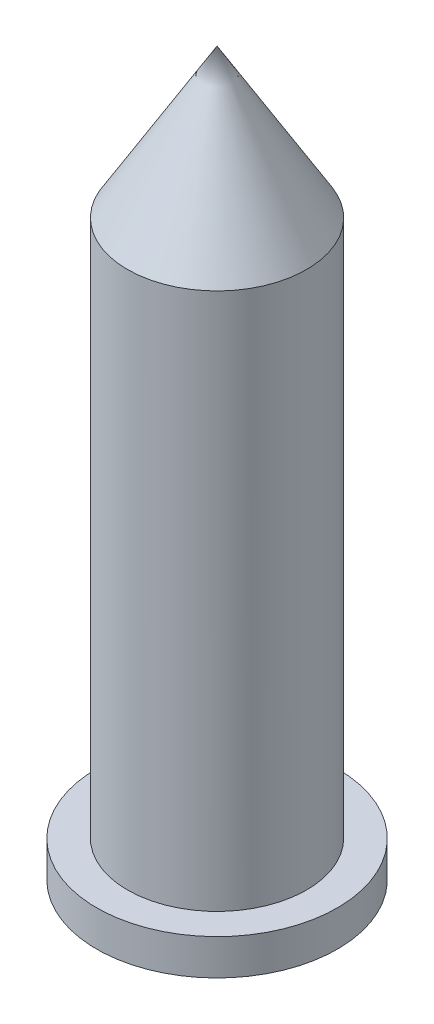
SolidWorks part; units mm, degrees
ref_plane "Front" through (0, 0, 0) normal (0, 0, 1) x (1, 0, 0)
ref_plane "Top" through (0, 0, 0) normal (0, 1, 0) x (1, 0, 0)
ref_plane "Right" through (0, 0, 0) normal (1, 0, 0) x (0, 0, -1)
sketch "Sketch1" plane through (0, 0, 0) normal (1, 0, 0) x (0, 0, -1)
  line L1 (-27.9083, 64.6906) -> (-22.9083, 64.6906)
  line L2 (-27.9083, 64.6906) -> (-27.9083, 34.6906)
  line L3 (-27.9083, 34.6906) -> (-22.9083, 34.6906)
  line L4 (-22.9083, 64.6906) -> (-22.9083, 34.6906)
  line L5 (-25.4083, 34.6906) -> (-25.4083, 64.6906) construction
  line L6 (-27.9083, 49.6906) -> (-22.9083, 49.6906) construction
  point P0 (-25.4083, 49.6906)
  dimension "D1" = 30
  dimension "D2" = 5
revolve "Revolve1" add sketch "Sketch1" angle 360 about L4
sketch "Sketch2" plane through (0, 0, 0) normal (1, 0, 0) x (0, 0, -1)
  line L0 (-17.9083, 64.6906) -> (-27.9083, 64.6906) construction
  line L1 (-27.9083, 64.6906) -> (-22.9083, 72.9987)
  line L2 (-22.9083, 72.9987) -> (-22.9083, 64.6906)
  line L3 (-22.9083, 64.6906) -> (-27.9083, 64.6906)
  dimension "D1" = 9.6966
  dimension "D2" = 8.3081
  dimension "D3" = 5
revolve "Revolve5" add sketch "Sketch2" angle 360 about L2
sketch "Sketch3" plane through (0, 34.6906, 0) normal (0, -1, 0) x (1, 0, 0)
  line L0 (0, 27.9083) -> (0, 17.9083) construction
  line L1 (-5, 22.9083) -> (5.8225, 22.9083) construction
  circle A1 centre (0, 22.9083) radius 5 construction
  circle A2 centre (0, 22.9083) radius 6.7218
  dimension "D3" = 6.7218
  dimension "D1" = 10
  dimension "D2" = 10.8225
extrude "Boss-Extrude1" add sketch "Sketch3" along normal blind 2
